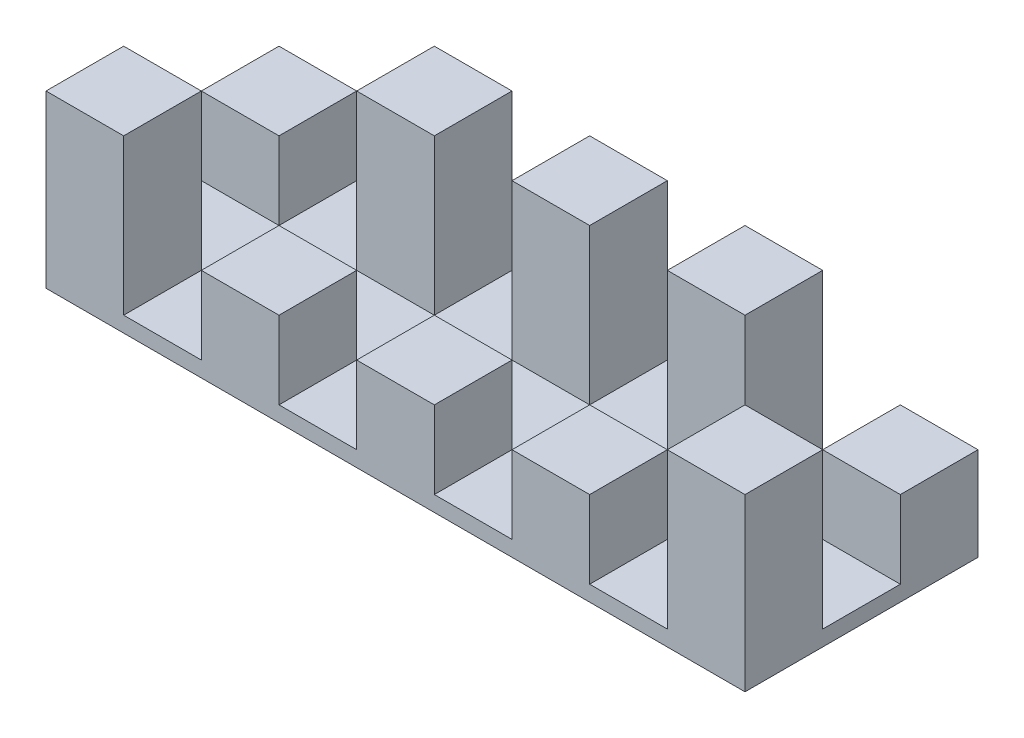
SolidWorks part; units mm, degrees
ref_plane "Front Plane" through (0, 0, 0) normal (0, 0, 1) x (1, 0, 0)
ref_plane "Top Plane" through (0, 0, 0) normal (0, 1, 0) x (1, 0, 0)
ref_plane "Right Plane" through (0, 0, 0) normal (1, 0, 0) x (0, 0, -1)
sketch "Sketch2" plane through (0, 0, 0) normal (0, 1, 0) x (1, 0, 0)
  line L0 (-175, 75) -> (-125, 75) construction
  line L1 (-225, 75) -> (225, 75)
  line L2 (-225, 75) -> (-225, -75)
  line L3 (-225, -75) -> (225, -75)
  line L4 (225, 75) -> (225, -75)
  line L5 (-225, 75) -> (225, -75) construction
  line L6 (-225, -75) -> (225, 75) construction
  line L7 (-225, 75) -> (-175, 75)
  line L8 (-225, 75) -> (-225, 25)
  line L9 (-225, 25) -> (-175, 25)
  line L10 (-175, 75) -> (-175, 25)
  line L11 (-225, -75) -> (-175, -75)
  line L12 (-225, -75) -> (-225, -25)
  line L13 (-225, -25) -> (-175, -25)
  line L14 (-175, -75) -> (-175, -25)
  line L15 (225, -75) -> (175, -75)
  line L16 (225, -75) -> (225, -25)
  line L17 (225, -75) -> (175, -75)
  line L18 (225, -75) -> (225, -25)
  line L19 (225, -25) -> (175, -25)
  line L20 (175, -75) -> (175, -25)
  line L21 (225, 75) -> (175, 75)
  line L22 (225, 75) -> (225, 25)
  line L23 (225, 25) -> (175, 25)
  line L24 (175, 75) -> (175, 25)
  line L25 (-125, 75) -> (-125, -75) construction
  line L26 (175, 75) -> (125, 75) construction
  line L27 (-125, 75) -> (-75, 75)
  line L28 (-125, 75) -> (-125, 25)
  line L29 (-125, 25) -> (-75, 25)
  line L30 (-75, 75) -> (-75, 25)
  line L31 (-125, -75) -> (-75, -75)
  line L32 (-125, -75) -> (-125, -25)
  line L33 (-125, -25) -> (-75, -25)
  line L34 (-75, -75) -> (-75, -25)
  line L35 (125, 75) -> (125, -75) construction
  line L36 (75, 75) -> (24.5793, 75) construction
  line L37 (125, 75) -> (75, 75)
  line L38 (125, 75) -> (125, 25)
  line L39 (125, 25) -> (75, 25)
  line L40 (75, 75) -> (75, 25)
  line L41 (125, -75) -> (75, -75)
  line L42 (125, -75) -> (125, -25)
  line L43 (125, -25) -> (75, -25)
  line L44 (75, -75) -> (75, -25)
  line L46 (24.5793, 75) -> (-25.4207, 75)
  line L47 (24.5793, 75) -> (24.5793, 25)
  line L48 (24.5793, 25) -> (-25.4207, 25)
  line L49 (-25.4207, 75) -> (-25.4207, 25)
  line L50 (-25.4207, -75) -> (24.5793, -75)
  line L51 (-25.4207, -75) -> (-25.4207, -25)
  line L52 (-25.4207, -25) -> (24.5793, -25)
  line L53 (24.5793, -75) -> (24.5793, -25)
  point P0 (0, 0)
  point P42 (0, 0)
  dimension "D1" = 450
  dimension "D2" = 150
  dimension "D3" = 50
  dimension "D4" = 50
  dimension "D5" = 50
  dimension "D6" = 50
  dimension "D7" = 50
  dimension "D8" = 50
  dimension "D9" = 50
extrude "Boss-Extrude4" add sketch "Sketch2" along normal blind 10 contours L53 L3 L44 L43 L42 L20 L19 L4 L23 L24 L1 L38 L39 L40 L47 L48 L49 L30 L29 L28 L10 L9 L2 L13 L14 L32 L33 L34 L51 L52 | L3 L14 L13 L2 | L3 L34 L33 L32 | L10 L1 L2 L9 | L30 L1 L28 L29 | L3 L53 L52 L51 | L1 L49 L48 L47 | L1 L40 L39 L38 | L44 L3 L42 L43 | L20 L3 L4 L19 | L1 L24 L23 L4
sketch "Sketch5" plane through (0, 10, 0) normal (0, 1, 0) x (1, 0, 0)
  line L1 (-225, 75) -> (-175, 75)
  line L2 (-225, 75) -> (-225, 25)
  line L3 (-225, 25) -> (-175, 25)
  line L4 (-175, 75) -> (-175, 25)
  line L5 (225, 75) -> (175, 75)
  line L6 (225, 75) -> (225, 25)
  line L7 (225, 25) -> (175, 25)
  line L8 (175, 75) -> (175, 25)
  dimension "D1" = 50
  dimension "D2" = 50
  dimension "D3" = 50
extrude "Boss-Extrude5" add sketch "Sketch5" along normal blind 50 contours L2 L1 L4 L3 | L6 L5 L8 L7
sketch "Sketch6" plane through (0, 10, 0) normal (0, 1, 0) x (1, 0, 0)
  line L1 (-225, -75) -> (-175, -75)
  line L2 (-225, -75) -> (-225, -25)
  line L3 (-225, -25) -> (-175, -25)
  line L4 (-175, -75) -> (-175, -25)
  line L5 (225, -75) -> (175, -75)
  line L6 (225, -75) -> (225, -25)
  line L7 (225, -25) -> (175, -25)
  line L8 (175, -75) -> (175, -25)
  dimension "D1" = 50
  dimension "D2" = 50
  dimension "D3" = 50
extrude "Boss-Extrude6" add sketch "Sketch6" along normal blind 100
sketch "Sketch7" plane through (0, 10, 0) normal (0, 1, 0) x (1, 0, 0)
  line L0 (-175, 75) -> (-125, 75) construction
  line L1 (-175, 75) -> (175, 75) construction
  line L2 (-75, 75) -> (-25, 75) construction
  line L3 (-125, 75) -> (-75, 75)
  line L4 (-125, 75) -> (-125, 25)
  line L5 (-125, 25) -> (-75, 25)
  line L6 (-75, 75) -> (-75, 25)
  line L7 (25, 75) -> (75, 75) construction
  line L8 (-25, 75) -> (25, 75)
  line L9 (-25, 75) -> (-25, 25)
  line L10 (-25, 25) -> (25, 25)
  line L11 (25, 75) -> (25, 25)
  line L13 (75, 75) -> (125, 75)
  line L14 (75, 75) -> (75, 25)
  line L15 (75, 25) -> (125, 25)
  line L16 (125, 75) -> (125, 25)
  dimension "D1" = 50
  dimension "D2" = 50
  dimension "D3" = 50
  dimension "D4" = 50
  dimension "D5" = 50
  dimension "D6" = 50
extrude "Boss-Extrude7" add sketch "Sketch7" along normal blind 100
sketch "Sketch8" plane through (0, 10, 0) normal (0, 1, 0) x (1, 0, 0)
  line L0 (-175, -75) -> (-125, -75) construction
  line L1 (-175, -75) -> (175, -75) construction
  line L2 (-125, -75) -> (-75, -75) construction
  line L3 (-75, -75) -> (-25, -75) construction
  line L4 (-25, -75) -> (25, -75) construction
  line L5 (25, -75) -> (75, -75) construction
  line L6 (75, -75) -> (125, -75) construction
  line L8 (-125, -75) -> (-75, -75)
  line L9 (-125, -75) -> (-125, -25)
  line L10 (-125, -25) -> (-75, -25)
  line L11 (-75, -75) -> (-75, -25)
  line L12 (-25, -75) -> (25, -75)
  line L13 (-25, -75) -> (-25, -25)
  line L14 (-25, -25) -> (25, -25)
  line L15 (25, -75) -> (25, -25)
  line L16 (75, -75) -> (125, -75)
  line L17 (75, -75) -> (75, -25)
  line L18 (75, -25) -> (125, -25)
  line L19 (125, -75) -> (125, -25)
  dimension "D1" = 50
extrude "Boss-Extrude8" add sketch "Sketch8" along normal blind 50
